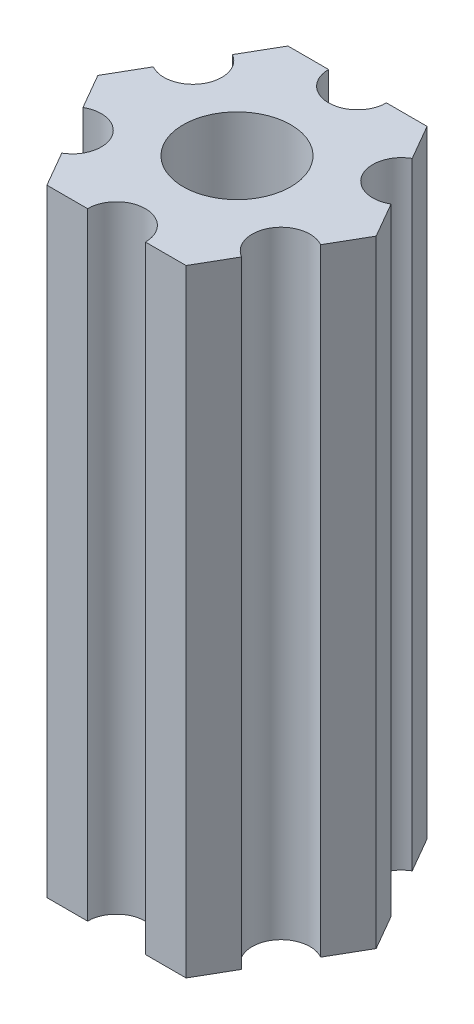
SolidWorks part; units mm, degrees
material "Churro - 6005A-T61"
ref_plane "Plano frontal" through (0, 0, 0) normal (0, 0, 1) x (1, 0, 0)
ref_plane "Plano superior" through (0, 0, 0) normal (0, 1, 0) x (1, 0, 0)
ref_plane "Plano direito" through (0, 0, 0) normal (1, 0, 0) x (0, 0, -1)
ref_plane "Plano1" through (0, 85, 0) normal (0, 1, 0) x (1, 0, 0)
sketch "Esboço1" plane through (0, 85, 0) normal (0, 1, 0) x (1, 0, 0)
  line L0 (6.1627, -1.826) -> (7.2169, 0)
  line L1 (7.2169, 0) -> (6.1627, 1.826)
  line L2 (4.6627, 4.424) -> (3.6084, 6.25)
  line L3 (3.6084, 6.25) -> (1.5, 6.25)
  line L4 (-1.5, 6.25) -> (-3.6084, 6.25)
  line L5 (-3.6084, 6.25) -> (-4.6627, 4.424)
  line L6 (-6.1627, 1.826) -> (-7.2169, 0)
  line L7 (-7.2169, 0) -> (-6.1627, -1.826)
  line L8 (-4.6627, -4.424) -> (-3.6084, -6.25)
  line L9 (-3.6084, -6.25) -> (-1.5, -6.25)
  line L10 (1.5, -6.25) -> (3.6084, -6.25)
  line L11 (3.6084, -6.25) -> (4.6627, -4.424)
  arc A0 (6.1627, 1.826) -> (4.6627, 4.424) centre (5.4127, 3.125) cw
  arc A1 (1.5, 6.25) -> (-1.5, 6.25) centre (0, 6.25) cw
  arc A2 (-4.6627, 4.424) -> (-6.1627, 1.826) centre (-5.4127, 3.125) cw
  arc A3 (-6.1627, -1.826) -> (-4.6627, -4.424) centre (-5.4127, -3.125) cw
  arc A4 (-1.5, -6.25) -> (1.5, -6.25) centre (0, -6.25) cw
  arc A5 (4.6627, -4.424) -> (6.1627, -1.826) centre (5.4127, -3.125) cw
  circle A6 centre (0, 0) radius 2.79
extrude "Ressalto-extrusão1" add sketch "Esboço1" against normal blind 32
